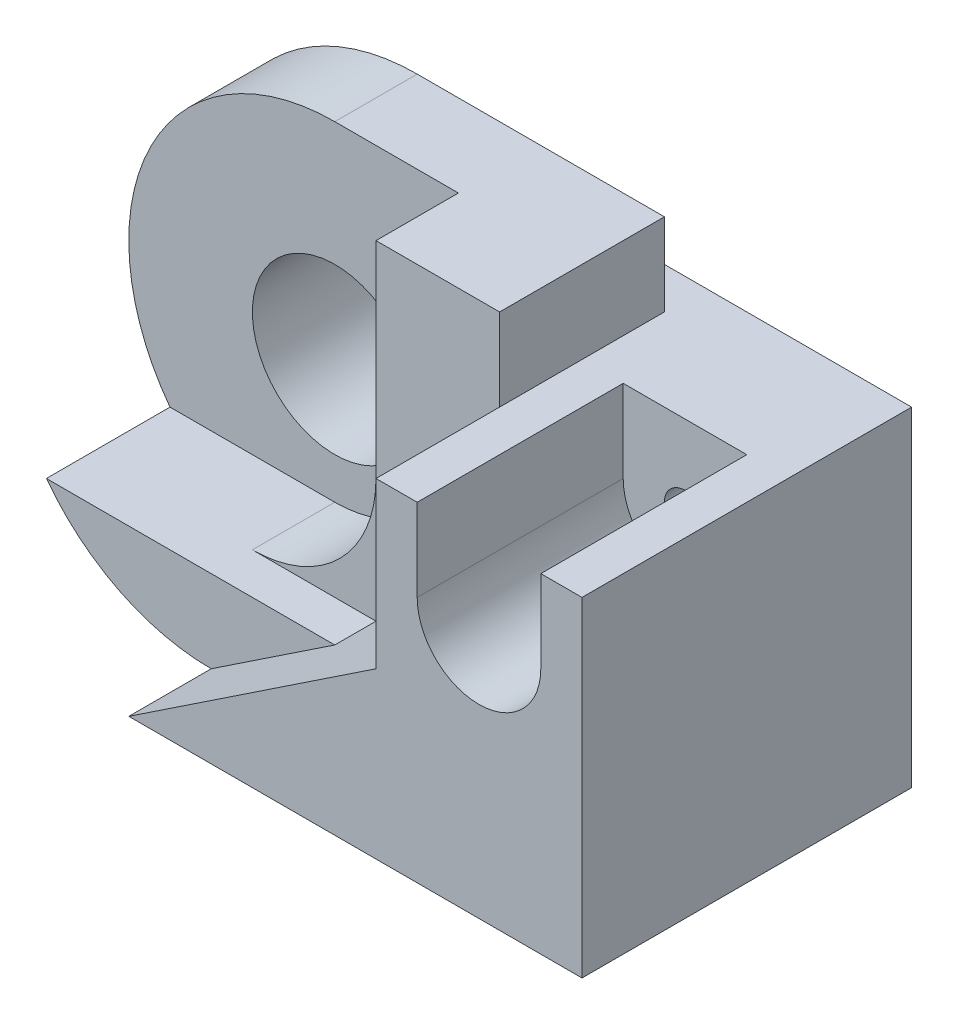
SolidWorks part; units mm, degrees
ref_plane "Front" through (0, 0, 0) normal (0, 0, 1) x (1, 0, 0)
ref_plane "Top" through (0, 0, 0) normal (0, 1, 0) x (1, 0, 0)
ref_plane "Right" through (0, 0, 0) normal (1, 0, 0) x (0, 0, -1)
sketch "Sketch1" plane through (0, 0, 0) normal (0, 0, 1) x (1, 0, 0)
  line L0 (0, 0) -> (11, 0)
  line L1 (11, 0) -> (11, 8)
  line L2 (11, 8) -> (6, 8)
  line L3 (6, 8) -> (6, 10)
  line L4 (6, 10) -> (0, 10)
  arc A0 (0, 10) -> (0, 0) centre (0, 5) ccw
  circle A1 centre (0, 5) radius 2
  dimension "D5" = 4
  dimension "D1" = 11
  dimension "D2" = 8
  dimension "D3" = 5
  dimension "D4" = 2
extrude "Boss-Extrude1" add sketch "Sketch1" along normal blind 3
sketch "Sketch2" plane through (6, 0, 0) normal (1, 0, 0) x (0, 0, -1)
  line L0 (-3, 10) -> (0, 10) construction
  line L1 (0, 8) -> (-1, 8)
  line L2 (0, 8) -> (0, 10)
  line L3 (0, 10) -> (-1, 10)
  line L4 (-1, 8) -> (-1, 10)
  dimension "D1" = 1
extrude "Cut-Extrude1" cut sketch "Sketch2" against normal blind 15
sketch "Sketch3" plane through (0, 0, 3) normal (0, 0, 1) x (1, 0, 0)
  line L0 (11, 8) -> (11, 0)
  line L1 (11, 0) -> (0, 0)
  line L2 (0, 0) -> (6, 4)
  line L3 (6, 4) -> (6, 8)
  line L4 (6, 8) -> (11, 8)
  circle A0 centre (8.5, 6) radius 0.5
  point P12 (0, 0)
  point P13 (0, 0)
  point P14 (0, 0)
  dimension "D1" = 4
extrude "Boss-Extrude2" add sketch "Sketch3" along normal blind 5
sketch "Sketch4" plane through (0, 0, 8) normal (0, 0, 1) x (1, 0, 0)
  line L0 (7, 8) -> (7, 6)
  line L1 (11, 8) -> (6, 8) construction
  line L2 (7, 8) -> (10, 8)
  line L3 (10, 8) -> (10, 6)
  line L4 (11, 0) -> (11, 8) construction
  arc A0 (10, 6) -> (7, 6) centre (8.5, 6) cw
  dimension "D3" = 1.5
  dimension "D1" = 3
  dimension "D2" = 2
  dimension "D4" = 2.5
extrude "Cut-Extrude2" cut sketch "Sketch4" against normal blind 5
sketch "Sketch5" plane through (0, 0, 3) normal (0, 0, 1) x (1, 0, 0)
  line L0 (3, 2) -> (-4, 2)
  line L1 (6, 4) -> (0, 0) construction
  line L2 (0, 0) -> (3, 2)
  arc A0 (0, 10) -> (0, 0) centre (0, 5) ccw construction
  arc A1 (-4, 2) -> (0, 0) centre (0, 5) ccw
  dimension "D1" = 2
extrude "Boss-Extrude3" add sketch "Sketch5" along normal blind 3
sketch "Sketch6" plane through (0, 0, 3) normal (0, 0, 1) x (1, 0, 0)
  line L0 (3, 10) -> (3, 5)
  line L1 (6, 10) -> (0, 10) construction
  line L3 (3, 2) -> (-4, 2) construction
  line L4 (0, 2) -> (3, 2)
  line L5 (6, 4) -> (0, 0) construction
  line L6 (3, 2) -> (6, 4)
  line L7 (6, 4) -> (6, 10)
  line L8 (6, 10) -> (3, 10)
  arc A0 (3, 5) -> (0, 2) centre (0, 5) cw
  dimension "D1" = 5
extrude "Boss-Extrude4" add sketch "Sketch6" along normal blind 2
sketch "Sketch7" plane through (0, 0, 3) normal (0, 0, 1) x (1, 0, 0)
  line L0 (7, 8) -> (7, 6) construction
  line L1 (10, 8) -> (7, 8) construction
  point P0 (8.5, 6)
  dimension "D1" = 1.5
  dimension "D2" = 2
hole_wizard "Ø1.0mm Dowel Hole1" positions "3DSketch1" profile "Sketch9" hole size "Ø1.0" standard "ISO"
sketch3d "3DSketch1"
  point P0 (8.5, 6, 3)
sketch "Sketch9" plane through (8.5, 6, 3) normal (1, 0, 0) x (0, -1, 0)
  line L0 (0, 0) -> (0, 2.3004)
  line L1 (0, 2.3004) -> (0.5, 2)
  line L2 (0.5, 2) -> (0.5, 0)
  line L5 (0.5, 0) -> (0, 0)
  line L10 (0, 2.3004) -> (-0.5, 2) construction
  line L11 (0, -6.35) -> (0, 107.95) construction
  dimension "Hole Dia." = 1
  dimension "Hole Depth" = 2
  dimension "Drill Angle" = 118
